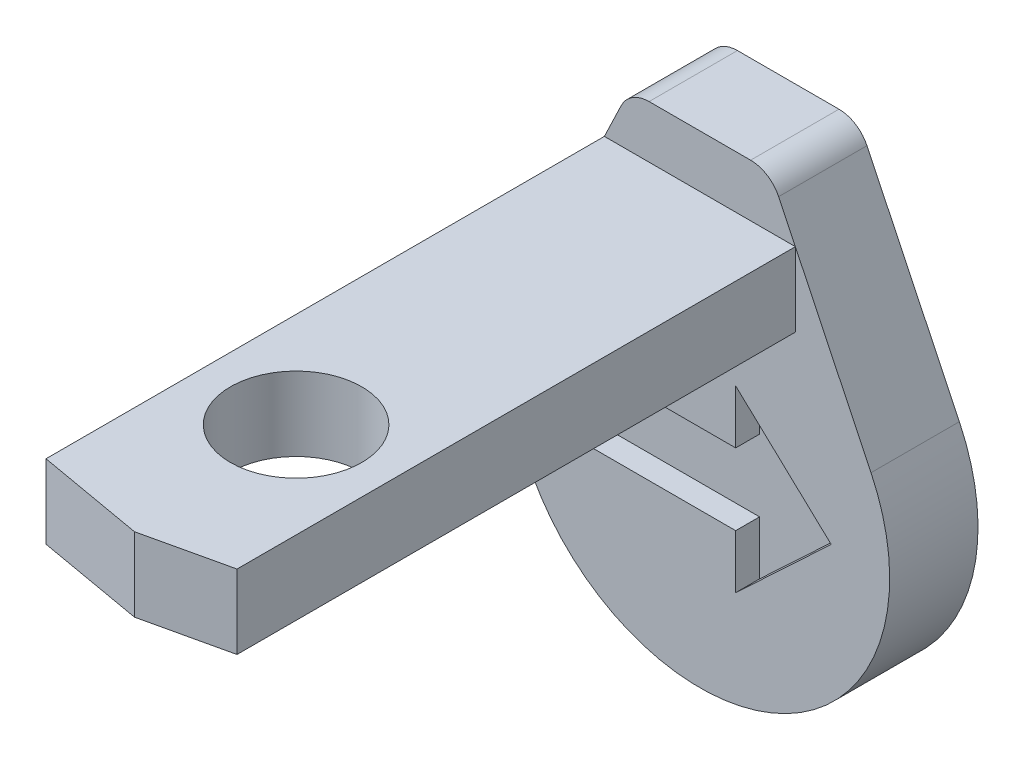
SolidWorks part; units mm, degrees
ref_plane "Front Plane" through (0, 0, 0) normal (0, 0, 1) x (1, 0, 0)
ref_plane "Top Plane" through (0, 0, 0) normal (0, 1, 0) x (1, 0, 0)
ref_plane "Right Plane" through (0, 0, 0) normal (1, 0, 0) x (0, 0, -1)
sketch "Sketch1" plane through (0, 0, 0) normal (0, 0, 1) x (1, 0, 0)
  line L0 (-32.9849, 92.6187) -> (-71.6911, 11.8604) construction
  line L1 (32.9849, 92.6187) -> (71.6911, 11.8604) construction
  line L2 (-32.9849, 92.6187) -> (-71.6911, 11.8604)
  line L3 (32.9849, 92.6187) -> (71.6911, 11.8604)
  line L4 (-21, 100) -> (21, 100) construction
  line L5 (-21.2619, 100) -> (21.2619, 100)
  arc A0 (4.7901, -101.8556) -> (79.3556, -27.2901) centre (0, -22.5) ccw construction
  circle A1 centre (0, -22.5) radius 79.5
  arc A2 (32.9849, 92.6187) -> (21.2619, 100) centre (21.2619, 87) ccw construction
  arc A3 (-21.2619, 100) -> (-32.9849, 92.6187) centre (-21.2619, 87) ccw construction
  arc A4 (32.9849, 92.6187) -> (21.2619, 100) centre (21.2619, 87) ccw
  arc A5 (-21.2619, 100) -> (-32.9849, 92.6187) centre (-21.2619, 87) ccw
extrude "Boss-Extrude1" add sketch "Sketch1" along normal up to surface (37 mm away) contours L5 A5 L2 A1 L3 A4 | A1
sketch "Sketch2" plane through (0, 0, 37) normal (0, 0, 1) x (1, 0, 0)
  line L5 (-40, 78) -> (-40, 47)
  line L6 (-40, 47) -> (40, 47)
  line L7 (40, 47) -> (40, 78)
  line L8 (40, 78) -> (-40, 78)
  line L9 (-40, 78) -> (-40, 47)
  line L10 (-40, 47) -> (40, 47)
  line L11 (40, 47) -> (40, 78)
  line L12 (40, 78) -> (-40, 78)
  dimension "D1" = 0
extrude "Boss-Extrude2" add sketch "Sketch2" along normal up to surface (212.65 mm away)
sketch "Sketch3" plane through (0, 78, 0) normal (0, 1, 0) x (1, 0, 0)
  line L0 (6.9641, -278.3394) -> (35, -271.9835) construction
  line L1 (5, -278.7847) -> (40, -270.85)
  line L2 (-35, -271.7316) -> (-23.1598, -273.8194) construction
  line L3 (-40, -270.85) -> (5, -278.7847)
  line L4 (-40, -260.75) -> (-40, -249.65) construction
  line L5 (-40, -270.85) -> (-40, -249.65)
  line L6 (40, -260.75) -> (40, -249.65) construction
  line L7 (40, -270.85) -> (40, -249.65)
  line L9 (40, -249.65) -> (-40, -249.65) construction
  line L10 (40, -249.65) -> (-40, -249.65)
extrude "Boss-Extrude3" add sketch "Sketch3" against normal up to surface (31 mm away) up to face at (0, 47, 143.325)
sketch "Sketch4" plane through (0, 0, 37) normal (0, 0, 1) x (1, 0, 0)
  line L0 (-79.5, -22.5) -> (79.5, -22.5) construction
  line L1 (55, -22.5) -> (15, 15)
  line L2 (15, 15) -> (15, -7.5)
  line L3 (15, -7.5) -> (-50, -7.5)
  line L4 (-50, -7.5) -> (-50, -37.5)
  line L5 (-50, -37.5) -> (15, -37.5)
  line L6 (15, -37.5) -> (15, -60)
  line L7 (15, -60) -> (55, -22.5)
  line L8 (15, -37.5) -> (15, -22.5) construction
  line L9 (15, -22.5) -> (15, -7.5) construction
  arc A0 (-71.6911, 11.8604) -> (71.6911, 11.8604) centre (0, -22.5) ccw construction
  dimension "D1" = 15
  dimension "D2" = 65
  dimension "D3" = 40
  dimension "D4" = 15
  dimension "D5" = 75
extrude "Cut-Extrude1" cut sketch "Sketch4" against normal blind 10
sketch "Sketch5" plane through (0, 78, 0) normal (0, 1, 0) x (1, 0, 0)
  circle A1 centre (0, -206.1) radius 27.5
  circle A2 centre (0, -206.1) radius 27.5
  dimension "D1" = 0
extrude "Cut-Extrude2" cut sketch "Sketch5" against normal through all
